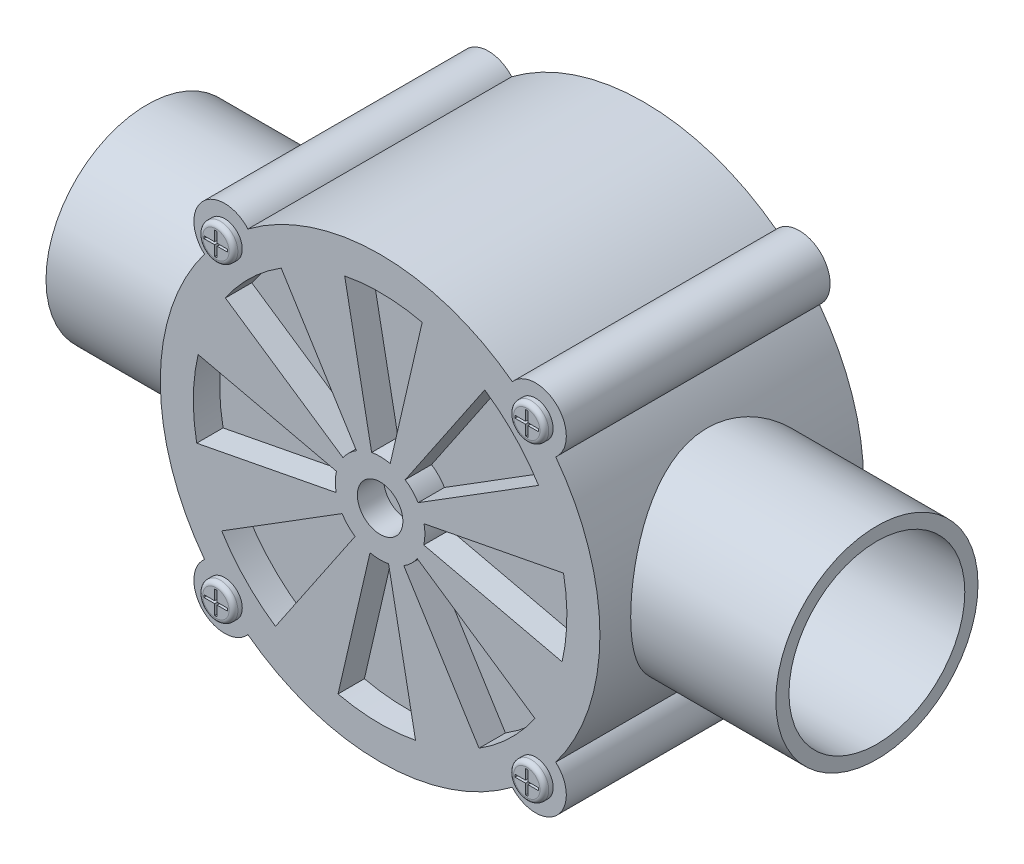
SolidWorks part; units mm, degrees
ref_plane "Alzado" through (0, 0, 0) normal (0, 0, 1) x (1, 0, 0)
ref_plane "Planta" through (0, 0, 0) normal (0, 1, 0) x (1, 0, 0)
ref_plane "Vista lateral" through (0, 0, 0) normal (1, 0, 0) x (0, 0, -1)
sketch "Croquis1" plane through (0, 0, 0) normal (0, 0, 1) x (1, 0, 0)
  circle A0 centre (0, 0) radius 25
  dimension "D1" = 50
extrude "Saliente-Extruir1" add sketch "Croquis1" along normal mid plane 30
sketch "Croquis2" plane through (0, 0, 15) normal (0, 0, 1) x (1, 0, 0)
  line L0 (0, 25) -> (0, -25) construction
  line L1 (-25, 0) -> (25, 0) construction
  line L2 (0, 0) -> (-17.6777, 17.6777) construction
  line L3 (0, 0) -> (17.6777, 17.6777) construction
  line L4 (0, 0) -> (17.6777, -17.6777) construction
  circle A0 centre (0, 0) radius 25 construction
  circle A1 centre (17.6777, 17.6777) radius 3.5
  circle A2 centre (17.6777, -17.6777) radius 3.5
  circle A3 centre (-17.6777, -17.6777) radius 3.5
  circle A4 centre (-17.6777, 17.6777) radius 3.5
  dimension "D1" = 7
extrude "Saliente-Extruir2" add sketch "Croquis2" against normal blind 30
sketch "Croquis3" plane through (0, 0, 15) normal (0, 0, 1) x (1, 0, 0)
  line L0 (1.1475, 4.9613) -> (4.7873, 20.698)
  line L1 (-0.9655, 4.9999) -> (-4.028, 20.8591)
  line L8 (0, 0) -> (15.7688, 15.7688) construction
  line L9 (0, 0) -> (25, 0) construction
  line L10 (2.8527, 4.2181) -> (11.9014, 17.5978)
  line L11 (4.3195, 2.6967) -> (18.0208, 11.2506)
  line L12 (4.9999, 0.9655) -> (20.8591, 4.028)
  line L13 (4.9613, -1.1475) -> (20.698, -4.7873)
  line L14 (4.2181, -2.8527) -> (17.5978, -11.9014)
  line L15 (2.6967, -4.3195) -> (11.2506, -18.0208)
  line L16 (0.9655, -4.9999) -> (4.028, -20.8591)
  line L17 (-1.1475, -4.9613) -> (-4.7873, -20.698)
  line L18 (-2.8527, -4.2181) -> (-11.9014, -17.5978)
  line L19 (-4.3195, -2.6967) -> (-18.0208, -11.2506)
  line L20 (-4.9999, -0.9655) -> (-20.8591, -4.028)
  line L21 (-4.9613, 1.1475) -> (-20.698, 4.7873)
  line L22 (-4.2181, 2.8527) -> (-17.5978, 11.9014)
  line L23 (-2.6967, 4.3195) -> (-11.2506, 18.0208)
  circle A0 centre (0, 0) radius 2.5874
  arc A1 (1.1475, 4.9613) -> (-0.9655, 4.9999) centre (0, 0) ccw
  arc A2 (4.7873, 20.698) -> (-4.028, 20.8591) centre (0, 0) ccw
  arc A12 (4.7873, 20.698) -> (-4.028, 20.8591) centre (0, 0) ccw
  arc A13 (18.0208, 11.2506) -> (11.9014, 17.5978) centre (0, 0) ccw
  arc A14 (4.3195, 2.6967) -> (2.8527, 4.2181) centre (0, 0) ccw
  arc A15 (1.1475, 4.9613) -> (-0.9655, 4.9999) centre (0, 0) ccw
  arc A17 (19.9732, -15.0356) -> (19.9732, 15.0356) centre (0, 0) ccw construction
  arc A18 (20.698, -4.7873) -> (20.8591, 4.028) centre (0, 0) ccw
  arc A19 (4.9613, -1.1475) -> (4.9999, 0.9655) centre (0, 0) ccw
  arc A20 (11.2506, -18.0208) -> (17.5978, -11.9014) centre (0, 0) ccw
  arc A21 (2.6967, -4.3195) -> (4.2181, -2.8527) centre (0, 0) ccw
  arc A22 (-4.7873, -20.698) -> (4.028, -20.8591) centre (0, 0) ccw
  arc A23 (-1.1475, -4.9613) -> (0.9655, -4.9999) centre (0, 0) ccw
  arc A24 (-18.0208, -11.2506) -> (-11.9014, -17.5978) centre (0, 0) ccw
  arc A25 (-4.3195, -2.6967) -> (-2.8527, -4.2181) centre (0, 0) ccw
  arc A26 (-20.698, 4.7873) -> (-20.8591, -4.028) centre (0, 0) ccw
  arc A27 (-4.9613, 1.1475) -> (-4.9999, -0.9655) centre (0, 0) ccw
  arc A28 (-11.2506, 18.0208) -> (-17.5978, 11.9014) centre (0, 0) ccw
  arc A29 (-2.6967, 4.3195) -> (-4.2181, 2.8527) centre (0, 0) ccw
  dimension "D1" = 8
extrude "Cortar-Extruir2" cut sketch "Croquis3" against normal blind 3 contours A14 L11 A13 L10 | A19 L13 A18 L12 | A21 L15 A20 L14 | A23 L17 A22 L16 | A25 L19 A24 L18 | A27 L21 A26 L20 | A29 L23 A28 L22 | L0 A2 L1 A1 | A0
mirror "Simetría1" about plane through (0, 0, 0) normal (0, 0, 1) of "Cortar-Extruir2"
sketch "Croquis5" plane through (0, 0, 0) normal (1, 0, 0) x (0, 0, -1)
  circle A0 centre (0, 0) radius 10
  circle A1 centre (0, 0) radius 11.5
  dimension "D1" = 20
  dimension "D2" = 23
extrude "Saliente-Extruir3" add sketch "Croquis5" along normal mid plane 83 contours A1 | A0
sketch "Croquis6" plane through (0, 0, 15) normal (0, 0, 1) x (1, 0, 0)
  line L0 (17.5369, 17.8223) -> (17.5369, 18.9815)
  line L1 (16.3376, 17.533) -> (17.5369, 17.533)
  line L2 (16.3376, 17.533) -> (16.3376, 17.8223)
  line L3 (16.3376, 17.8223) -> (17.5369, 17.8223)
  line L4 (19.0177, 17.533) -> (19.0177, 17.8223)
  line L5 (17.8184, 17.533) -> (19.0177, 17.533)
  line L6 (0, 0) -> (20.2834, 0) construction
  line L7 (17.8184, 16.3739) -> (17.5369, 16.3739)
  line L8 (17.8184, 16.3739) -> (17.8184, 17.533)
  line L9 (17.8184, 18.9815) -> (17.5369, 18.9815)
  line L10 (17.5369, 16.3739) -> (17.5369, 17.533)
  line L11 (0, 0) -> (0, 17.8223) construction
  line L12 (17.8184, -16.3739) -> (17.8184, -17.533)
  line L13 (17.8184, -17.533) -> (19.0177, -17.533)
  line L14 (19.0177, -17.533) -> (19.0177, -17.8223)
  line L15 (17.8184, -17.8223) -> (19.0177, -17.8223)
  line L17 (17.8184, 17.8223) -> (17.8184, 18.9815)
  line L18 (17.8184, 17.8223) -> (19.0177, 17.8223)
  line L19 (17.8184, -17.8223) -> (17.8184, -18.9815)
  line L20 (17.8184, -18.9815) -> (17.5369, -18.9815)
  line L21 (17.5369, -17.8223) -> (17.5369, -18.9815)
  line L22 (16.3376, -17.8223) -> (17.5369, -17.8223)
  line L23 (16.3376, -17.533) -> (16.3376, -17.8223)
  line L24 (16.3376, -17.533) -> (17.5369, -17.533)
  line L25 (17.5369, -16.3739) -> (17.5369, -17.533)
  line L26 (17.8184, -16.3739) -> (17.5369, -16.3739)
  line L27 (-17.8184, -16.3739) -> (-17.5369, -16.3739)
  line L28 (-17.5369, -16.3739) -> (-17.5369, -17.533)
  line L29 (-16.3376, -17.533) -> (-17.5369, -17.533)
  line L30 (-16.3376, -17.533) -> (-16.3376, -17.8223)
  line L31 (-16.3376, -17.8223) -> (-17.5369, -17.8223)
  line L32 (-17.5369, -17.8223) -> (-17.5369, -18.9815)
  line L33 (-17.8184, -18.9815) -> (-17.5369, -18.9815)
  line L34 (-17.8184, -17.8223) -> (-17.8184, -18.9815)
  line L35 (-17.8184, -17.8223) -> (-19.0177, -17.8223)
  line L36 (-19.0177, -17.533) -> (-19.0177, -17.8223)
  line L37 (-17.8184, -17.533) -> (-19.0177, -17.533)
  line L38 (-17.8184, -16.3739) -> (-17.8184, -17.533)
  line L39 (-17.8184, 16.3739) -> (-17.8184, 17.533)
  line L40 (-17.8184, 17.533) -> (-19.0177, 17.533)
  line L41 (-19.0177, 17.533) -> (-19.0177, 17.8223)
  line L42 (-17.8184, 17.8223) -> (-19.0177, 17.8223)
  line L43 (-17.8184, 17.8223) -> (-17.8184, 18.9815)
  line L44 (-17.8184, 18.9815) -> (-17.5369, 18.9815)
  line L45 (-17.5369, 17.8223) -> (-17.5369, 18.9815)
  line L46 (-16.3376, 17.8223) -> (-17.5369, 17.8223)
  line L47 (-16.3376, 17.533) -> (-16.3376, 17.8223)
  line L48 (-16.3376, 17.533) -> (-17.5369, 17.533)
  line L49 (-17.5369, 16.3739) -> (-17.5369, 17.533)
  line L50 (-17.8184, 16.3739) -> (-17.5369, 16.3739)
  circle A0 centre (17.6777, 17.6777) radius 2
  circle A1 centre (17.6777, -17.6777) radius 2
  circle A2 centre (-17.6777, -17.6777) radius 2
  circle A3 centre (-17.6777, 17.6777) radius 2
  dimension "D1" = 4
extrude "Saliente-Extruir4" add sketch "Croquis6" along normal blind 1
fillet "Redondeo1" radius 0.5 4 edges at (15.6777, -17.6777, 16) (-15.6777, -17.6777, 16) (19.6777, 17.6777, 16) (-19.6777, 17.6777, 16)
